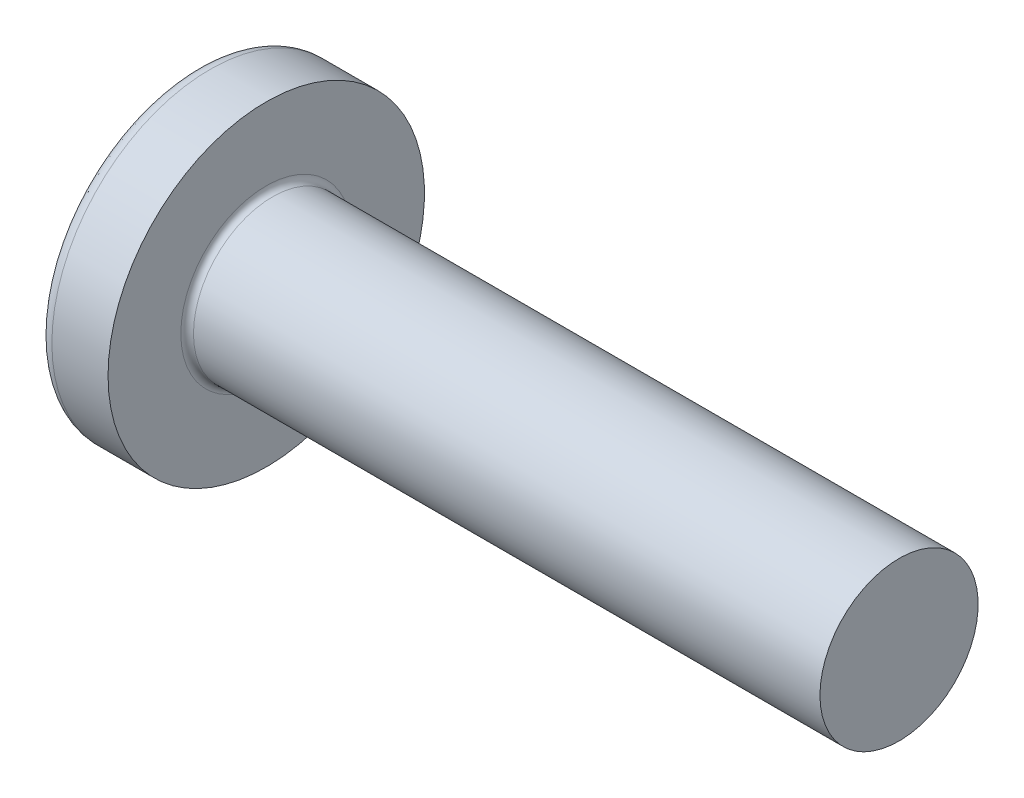
SolidWorks part; units mm, degrees
ref_plane "Plane1" through (0, 0, 0) normal (0, 0, 1) x (1, 0, 0)
ref_plane "Plane2" through (0, 0, 0) normal (0, 1, 0) x (1, 0, 0)
ref_plane "Plane3" through (0, 0, 0) normal (1, 0, 0) x (0, 0, -1)
sketch "BodySke" plane through (0, 0, 0) normal (0, 0, 1) x (1, 0, 0)
  line L0 (7.5, 5) -> (7.5, 10)
  line L1 (8.25, 6.35) -> (8.25, -3.175) construction
  line L2 (-25.4, 0) -> (127, 0) construction
  line L3 (47.5, 0) -> (0, 0)
  line L4 (7.5, 5) -> (47.5, 5)
  line L5 (47.5, 5) -> (47.5, 0)
  line L6 (3.9501, 10) -> (7.5, 10)
  line L8 (7.5, 6.35) -> (7.5, -3.175) construction
  arc A0 (3.2319, 9.6424) -> (0, 0) centre (16, 0) ccw
  arc A2 (3.2319, 9.6424) -> (3.9501, 10) centre (3.9501, 9.1) cw
  dimension "Head_fillet_rad" = 0.9
  dimension "Head_crown_rad" = 16
  dimension "Head_ht" = 7.5
  dimension "Diameter" = 10
  dimension "Length" = 40
  dimension "Head_dia" = 20
  dimension "Advance" = 1.5
  dimension "Thread_nom" = 40
revolve "Base-Revolve" add sketch "BodySke"
cosmetic thread "ThreadCosmetic"
fillet "Fillet1" radius 0.4 1 edges at (7.5, 0, 5)
sketch "Sketch3" plane through (0, 0, 0) normal (1, 0, 0) x (0, 0, -1)
  line L0 (1.08, -4.95) -> (-1.08, -4.95)
  line L1 (1.08, -4.95) -> (1.08, 4.95)
  line L2 (-1.08, 4.95) -> (1.08, 4.95)
  line L3 (-1.08, 4.95) -> (-1.08, -4.95)
  dimension "D1" = 3.35
  dimension "Cross_dia" = 9.9
  dimension "D2" = 0.71
  dimension "Cross_width" = 2.16
ref_plane "Plane4" through (5.69, 0, 0) normal (1, 0, 0) x (0, 0, -1)
sketch "Sketch4" plane through (5.69, 0, 0) normal (1, 0, 0) x (0, 0, -1)
  line L0 (1.08, -2.1131) -> (-1.08, -2.1131)
  line L1 (1.08, -2.1131) -> (1.08, 2.1131)
  line L2 (-1.08, 2.1131) -> (1.08, 2.1131)
  line L3 (-1.08, 2.1131) -> (-1.08, -2.1131)
  dimension "D1" = 1.42
  dimension "D2" = 3.2498
  dimension "D3" = 0.71
  dimension "D4" = 1.6249
loft "Recess" cut profiles "Sketch3", "Sketch4"
pattern_circular "RecPat" count 2 every 90 about axis through (0, 0, 0) along (1, 0, 0) of "Recess"
sketch "RecCorSke" plane through (0, 0, 0) normal (0, 0, 1) x (1, 0, 0)
  line L0 (-3.175, 0) -> (15.875, 0) construction
  line L1 (-25.4, 0) -> (127, 0) construction
  line L2 (0, 0) -> (0, 2.3284)
  line L3 (0, 2.3284) -> (5.69, 1.9305)
  line L4 (5.69, 1.9305) -> (6.3173, 0)
  line L5 (6.3173, 0) -> (0, 0)
  dimension "Diameter" = 3.861
  dimension "Depth" = 3.46
  dimension "Draft_angle" = 4
  dimension "Bottom_angle" = 18
revolve "RecessCore" cut sketch "RecCorSke" angle 360 about L0
sketch "ThdSchSke" plane through (0, 0, 0) normal (0, 0, 1) x (1, 0, 0)
  line L0 (10.5, -4.172) -> (9.9202, -5)
  line L1 (10.5, -4.172) -> (11.0798, -5)
  line L2 (11.0798, -5) -> (11.0798, -6.25)
  line L3 (-3.175, 0) -> (5.1513, 0) construction
  line L5 (11.0798, -6.25) -> (9.9202, -6.25)
  line L6 (9.9202, -6.25) -> (9.9202, -5)
  dimension "Thread_minor" = 4.891
  dimension "Diameter" = 6
  dimension "Start" = 6.6
  dimension "SideAngle" = 55
  dimension "VeeAngle" = 70
  dimension "Overcut" = 7.5
revolve "ThreadSchematic" [suppressed] cut sketch "ThdSchSke" angle 360 about L3
pattern_linear "ThdSchPat" [suppressed]
equation "\"D1@Sketch3\" = \"Cross_dia@Sketch3\" / 2"
equation "\"D2@Sketch3\" = \"Cross_width@Sketch3\" / 2"
equation "\"Depth@RecCorSke\" = \"Cross_depth@Plane4\""
equation "\"D1@Sketch4\" = \"Cross_width@Sketch3\""
equation "\"D2@Sketch4\" = \"Cross_dia@Sketch3\" - 2.0 * \"Cross_depth@Plane4\" * tan(26.5  * 0.017453292)"
equation "\"D3@Sketch4\" = \"D1@Sketch4\" / 2"
equation "\"D4@Sketch4\" = \"D2@Sketch4\" / 2"
equation "\"Thread_length@ThreadCosmetic\" = ((sgn( (\"Length@BodySke\" - \"Advance@BodySke\" * 2.0 ) - \"Thread_nom@BodySke\" )-1)*( (\"Length@BodySke\" - \"Advance@BodySke\" * 2.0 ) - \"Thread_nom@BodySke\" ))/-2+ \"Thread_nom@BodySke\""
equation "\"Thread_minor@ThdSchSke\" = \"Thread_minor@ThreadCosmetic\""
equation "\"Diameter@ThdSchSke\" = \"Diameter@BodySke\""
equation "\"Overcut@ThdSchSke\" = \"Diameter@BodySke\" * 1.25"
equation "\"Start@ThdSchSke\" = \"Head_ht@BodySke\" + \"Length@BodySke\" - \"Thread_length@ThreadCosmetic\"  '---Non-countersunk---"
equation "\"Num_threads@ThdSchPat\" = int( \"Thread_length@ThreadCosmetic\" / \"Advance@BodySke\" + 0.999 )  + 1"
equation "\"Advance@ThdSchPat\" = \"Thread_length@ThreadCosmetic\" /  (\"Num_threads@ThdSchPat\" - 1) 'relax it"
